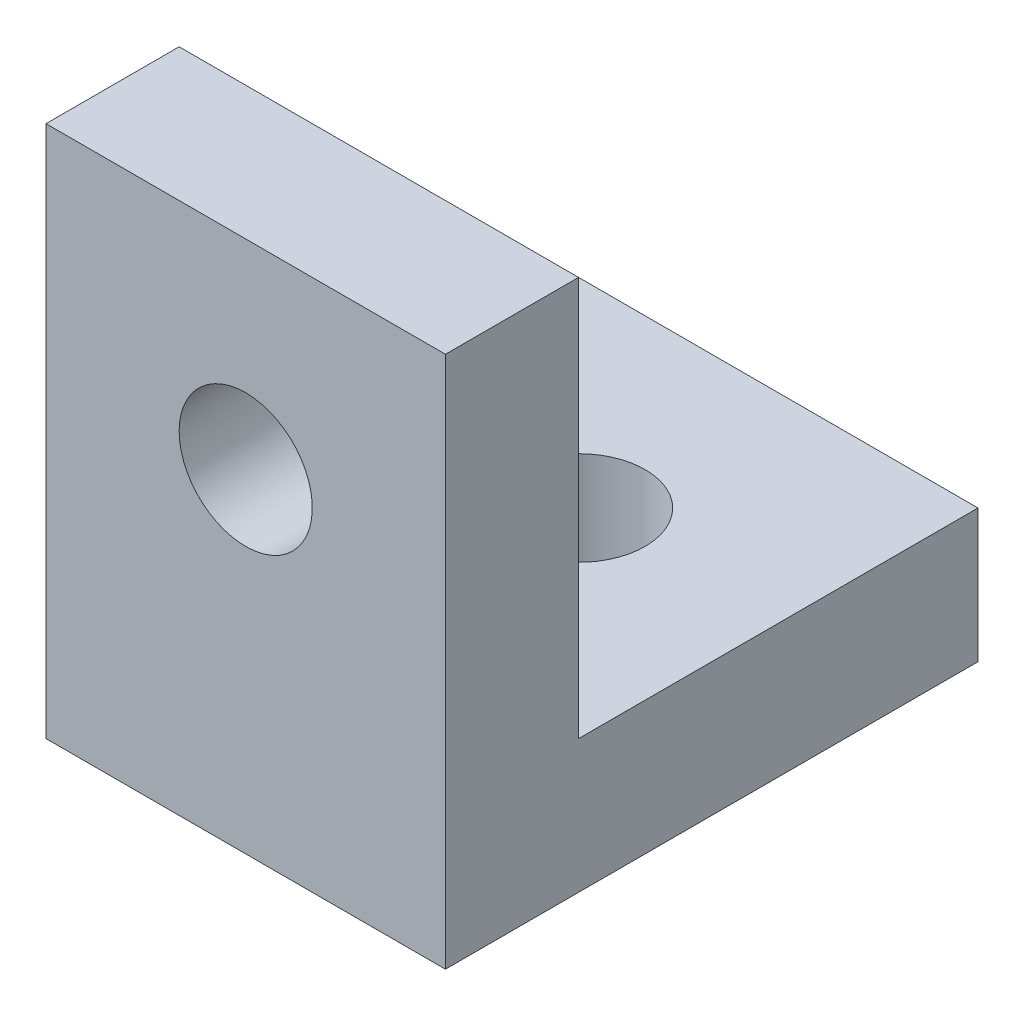
SolidWorks part; units mm, degrees
ref_plane "Front Plane" through (0, 0, 0) normal (0, 0, 1) x (1, 0, 0)
ref_plane "Top Plane" through (0, 0, 0) normal (0, 1, 0) x (1, 0, 0)
ref_plane "Right Plane" through (0, 0, 0) normal (1, 0, 0) x (0, 0, -1)
sketch "Sketch1" plane through (0, 0, 0) normal (1, 0, 0) x (0, 0, -1)
  line L0 (0, 0) -> (0, 40)
  line L1 (0, 40) -> (10, 40)
  line L2 (10, 40) -> (10, 10)
  line L3 (10, 10) -> (40, 10)
  line L4 (40, 10) -> (40, 0)
  line L5 (40, 0) -> (0, 0)
  dimension "D1" = 10
  dimension "D2" = 40
  dimension "D3" = 40
  dimension "D4" = 10
extrude "Boss-Extrude1" add sketch "Sketch1" along normal blind 30
sketch "Sketch2" plane through (0, 0, -10) normal (0, 0, -1) x (-1, 0, 0)
  line L0 (-30, 0) -> (0, 0) construction
  line L1 (-30, 10) -> (-30, 40) construction
  circle A0 centre (-15, 25) radius 5
  dimension "D1" = 10
  dimension "D2" = 25
  dimension "D3" = 15
extrude "Cut-Extrude1" cut sketch "Sketch2" against normal blind 30
sketch "Sketch3" plane through (0, 10, 0) normal (0, 1, 0) x (1, 0, 0)
  line L0 (30, 0) -> (0, 0) construction
  line L1 (0, 40) -> (0, 10) construction
  circle A0 centre (15, 25) radius 5
  dimension "D1" = 10
  dimension "D2" = 25
  dimension "D3" = 15
extrude "Cut-Extrude2" cut sketch "Sketch3" against normal blind 30
